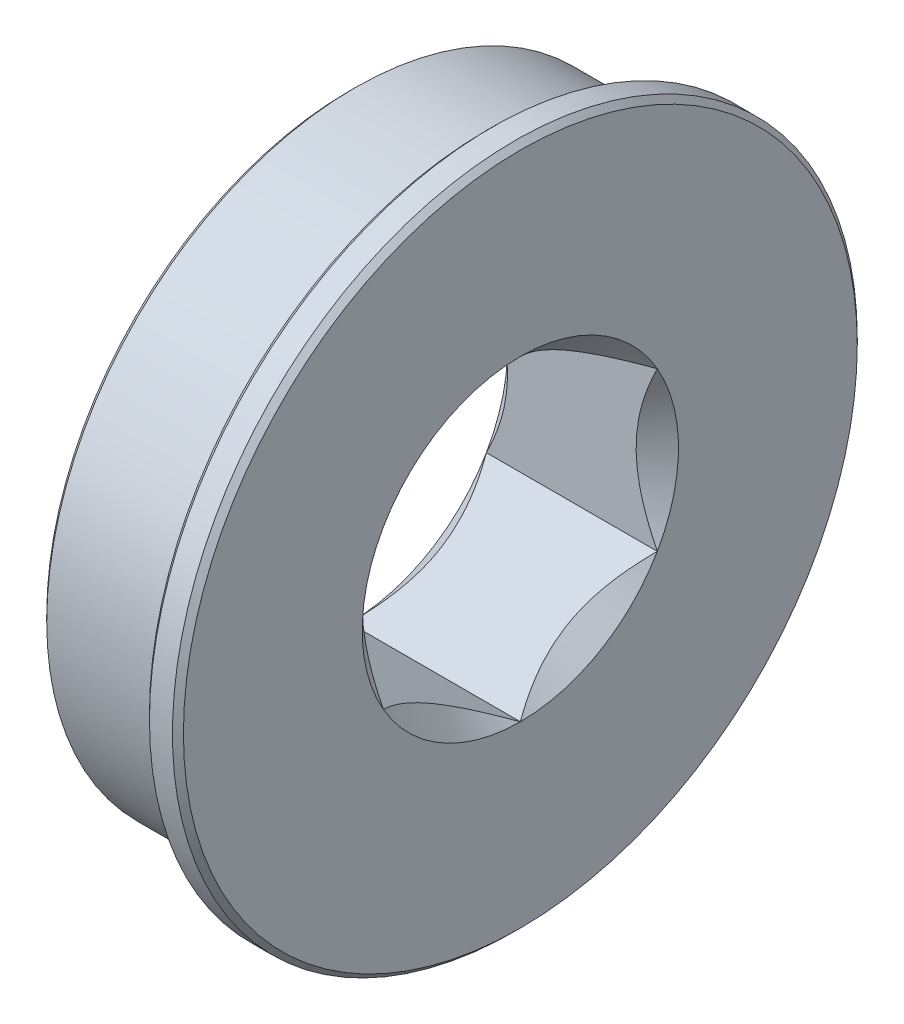
SolidWorks part; units mm, degrees
ref_plane "Front Plane" through (0, 0, 0) normal (0, 0, 1) x (1, 0, 0)
ref_plane "Top Plane" through (0, 0, 0) normal (0, 1, 0) x (1, 0, 0)
ref_plane "Right Plane" through (0, 0, 0) normal (1, 0, 0) x (0, 0, -1)
sketch "Sketch1" plane through (0, 0, 0) normal (0, 0, 1) x (1, 0, 0)
  line L0 (3.9624, 0) -> (-3.9624, 0) construction
  line L1 (-3.9624, 0) -> (-3.9624, 14.2875) construction
  line L2 (-3.9624, 14.2875) -> (2.3876, 14.2875)
  line L3 (2.3876, 14.2875) -> (2.3876, 15.875)
  line L4 (2.3876, 15.875) -> (3.9624, 15.875)
  line L5 (3.9624, 15.875) -> (3.9624, 0) construction
  line L6 (3.9624, 15.875) -> (3.9624, 7.3323)
  line L7 (3.9624, 6.35) -> (-3.9624, 6.35) construction
  line L8 (-3.9624, 7.3323) -> (-3.9624, 14.2875)
  line L9 (3.9624, 7.3323) -> (2.9801, 6.35)
  line L10 (2.9801, 6.35) -> (-2.9801, 6.35)
  line L11 (-2.9801, 6.35) -> (-3.9624, 7.3323)
  line L12 (0.7874, 5.4993) -> (3.9624, 7.3323) construction
  line L13 (7.1374, 5.4993) -> (3.9624, 7.3323) construction
  circle A0 centre (3.9624, 0) radius 6.35 construction
  point P4 (0, 0)
  point P17 (7.1273, 5.5051)
  dimension "D1" = 7.9248
  dimension "D2" = 6.35
  dimension "D3" = 28.575
  dimension "D4" = 31.75
  dimension "D5" = 1.5748
  dimension "D6" = 45
  dimension "D7" = 60
revolve "Revolve1" add sketch "Sketch1" angle 360 about L0
sketch "Sketch2" plane through (3.9624, 0, 0) normal (1, 0, 0) x (0, 0, -1)
  line L1 (0, 7.3323) -> (-6.35, 3.6662)
  line L2 (-6.35, 3.6662) -> (-6.35, -3.6662)
  line L3 (-6.35, -3.6662) -> (0, -7.3323)
  line L4 (0, -7.3323) -> (6.35, -3.6662)
  line L5 (6.35, -3.6662) -> (6.35, 3.6662)
  line L6 (6.35, 3.6662) -> (0, 7.3323)
  circle A0 centre (0, 0) radius 6.35 construction
  circle A2 centre (0, 0) radius 6.35 construction
extrude "Cut-Extrude1" cut sketch "Sketch2" against normal through all
chamfer "Chamfer1" distance 0.254 angle 45 3 edges at (3.9624, 0, -15.875) (2.3876, 0, -15.875) (-3.9624, 0, -14.2875)
